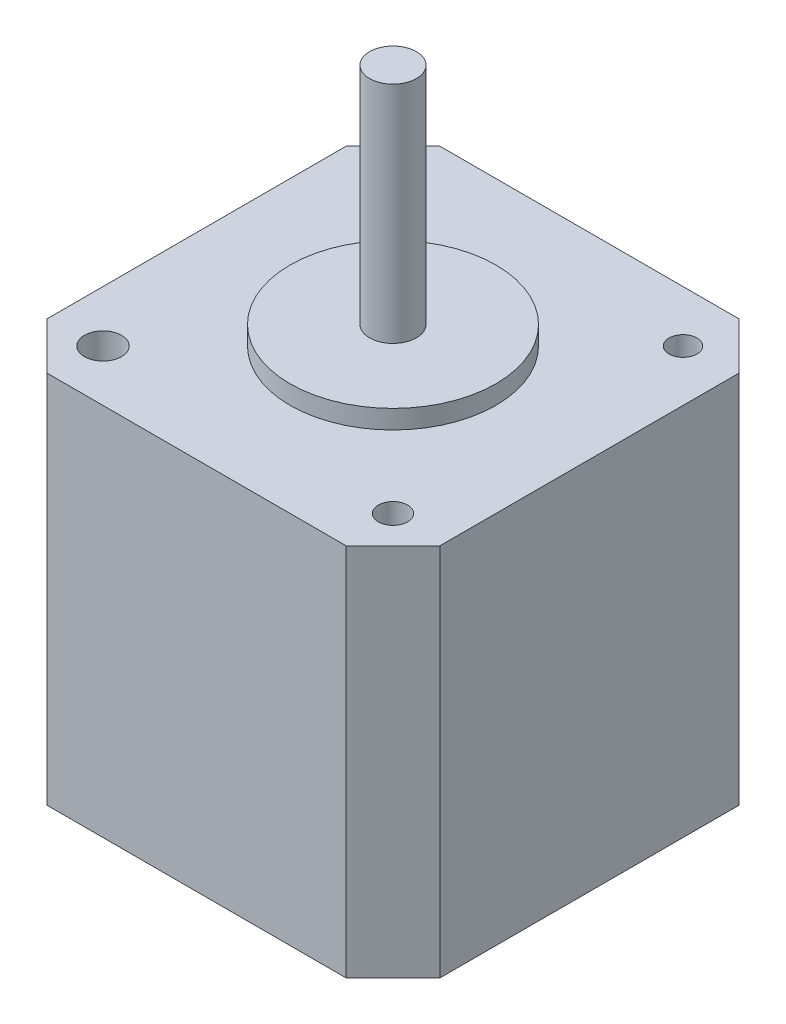
SolidWorks part; units mm, degrees
ref_plane "Front Plane" through (0, 0, 0) normal (0, 0, 1) x (1, 0, 0)
ref_plane "Top Plane" through (0, 0, 0) normal (0, 1, 0) x (1, 0, 0)
ref_plane "Right Plane" through (0, 0, 0) normal (1, 0, 0) x (0, 0, -1)
sketch "Sketch1" plane through (0, 0, 0) normal (0, 1, 0) x (1, 0, 0)
  line L1 (21, -21) -> (-21, -21)
  line L2 (21, -21) -> (21, 21)
  line L3 (21, 21) -> (-21, 21)
  line L4 (-21, -21) -> (-21, 21)
  line L5 (21, -21) -> (-21, 21) construction
  line L6 (21, 21) -> (-21, -21) construction
  point P0 (0, 0)
  dimension "D1" = 42
  dimension "42" = 42
extrude "Boss-Extrude1" add sketch "Sketch1" along normal blind 40
chamfer "Chamfer1" distance 5 angle 45 4 edges at (-21, 20, 21) (-21, 20, -21) (21, 20, 21) (21, 20, -21)
sketch "Sketch2" plane through (0, 40, 0) normal (0, 1, 0) x (1, 0, 0)
  circle A0 centre (0, 0) radius 11
  dimension "D1" = 22
extrude "Boss-Extrude2" add sketch "Sketch2" along normal blind 2
sketch "Sketch3" plane through (0, 40, 0) normal (0, 1, 0) x (1, 0, 0)
  line L1 (15.5, -15.5) -> (-15.5, -15.5) construction
  line L2 (15.5, -15.5) -> (15.5, 15.5) construction
  line L3 (15.5, 15.5) -> (-15.5, 15.5) construction
  line L4 (-15.5, -15.5) -> (-15.5, 15.5) construction
  line L5 (15.5, -15.5) -> (-15.5, 15.5) construction
  line L6 (15.5, 15.5) -> (-15.5, -15.5) construction
  circle A0 centre (15.5, 15.5) radius 1.49
  circle A1 centre (15.5, -15.5) radius 1.5619
  circle A2 centre (-15.5, -15.5) radius 1.9811
  circle A3 centre (-15.5, 15.5) radius 1.5828
  point P0 (0, 0)
  dimension "D1" = 31
  dimension "D2" = 31
extrude "Cut-Extrude1" cut sketch "Sketch3" against normal blind 8
sketch "Sketch4" plane through (0, 42, 0) normal (0, 1, 0) x (1, 0, 0)
  circle A0 centre (0, 0) radius 2.5
  dimension "D1" = 5
extrude "Boss-Extrude3" add sketch "Sketch4" along normal blind 24
